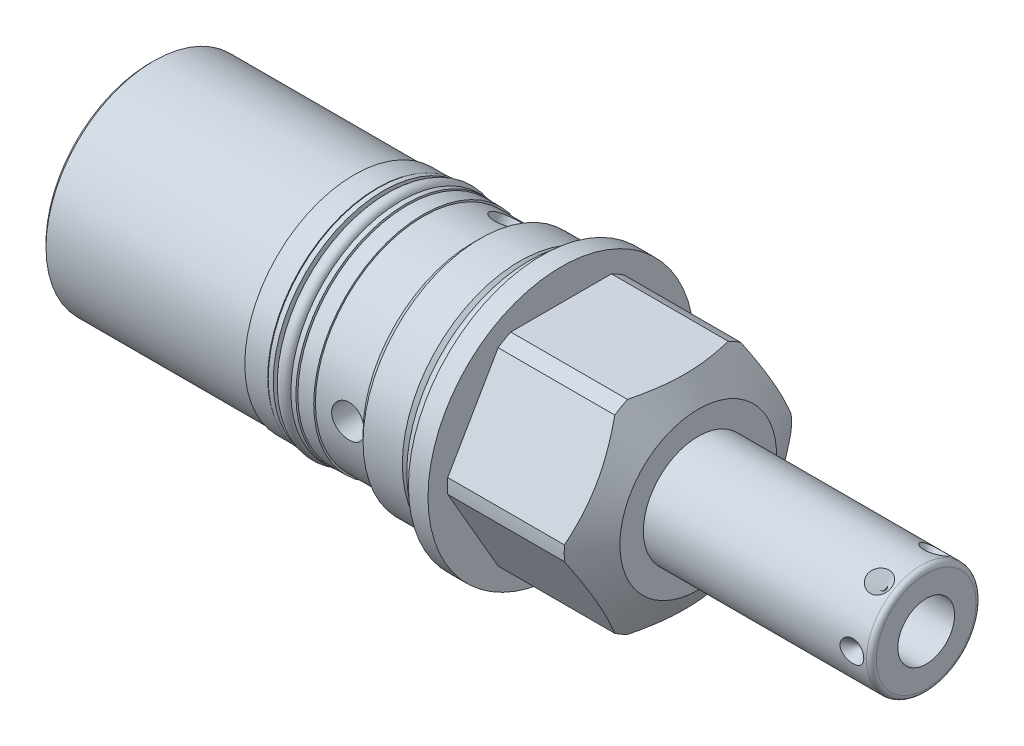
SolidWorks part; units mm, degrees
material "Alloy Steel"
ref_plane "Front Plane" through (0, 0, 0) normal (0, 0, 1) x (1, 0, 0)
ref_plane "Top Plane" through (0, 0, 0) normal (0, 1, 0) x (1, 0, 0)
ref_plane "Right Plane" through (0, 0, 0) normal (1, 0, 0) x (0, 0, -1)
sketch "Sketch1" plane through (0, 0, 0) normal (0, 0, 1) x (1, 0, 0)
  line L0 (0, 0) -> (113.8544, 0) construction
  line L1 (0, 26.9875) -> (3.9624, 26.9875)
  line L2 (3.9624, 26.9875) -> (3.9624, 23.0251)
  line L3 (3.9624, 23.0251) -> (27.6219, 23.0251)
  line L4 (27.6219, 23.0251) -> (31.75, 15.875)
  line L5 (31.75, 15.875) -> (31.75, 0)
  line L6 (31.75, 0) -> (-79.375, 0)
  line L7 (-79.375, 0) -> (-79.375, 21.844)
  line L8 (0, 26.9875) -> (0, 22.3012)
  line L9 (0, 22.3012) -> (-2.8956, 22.3012)
  line L10 (-2.8956, 22.3012) -> (-4.4069, 23.8125)
  line L11 (-4.4069, 23.8125) -> (-12.3698, 23.8125)
  line L12 (-12.3698, 23.8125) -> (-13.9954, 22.1869)
  line L14 (-13.9954, 22.1869) -> (-13.9954, 21.844)
  line L15 (-13.9954, 21.844) -> (-79.375, 21.844)
  dimension "D1" = 53.975
  dimension "D2" = 31.75
  dimension "D3" = 3.9624
  dimension "D4" = 31.75
  dimension "D5" = 46.0502
  dimension "D6" = 30
  dimension "D7" = 79.375
  dimension "D8" = 76.4794
  dimension "D9" = 44.6024
  dimension "D10" = 45
  dimension "D11" = 47.625
  dimension "D12" = 11.0998
  dimension "D13" = 44.3738
  dimension "D14" = 43.688
revolve "Revolve1" add sketch "Sketch1" angle 360 about L0
sketch "Sketch2" plane through (31.75, 0, 0) normal (1, 0, 0) x (0, 0, -1)
  line L1 (11.9151, 20.6375) -> (-11.9151, 20.6375)
  line L2 (-11.9151, 20.6375) -> (-23.8301, 0)
  line L3 (-23.8301, 0) -> (-11.9151, -20.6375)
  line L4 (-11.9151, -20.6375) -> (11.9151, -20.6375)
  line L5 (11.9151, -20.6375) -> (23.8301, 0)
  line L6 (23.8301, 0) -> (11.9151, 20.6375)
  circle A0 centre (0, 0) radius 20.6375 construction
  dimension "D1" = 41.275
extrude "Cut-Extrude1" cut sketch "Sketch2" against normal up to surface (27.7876 mm away) flip side to cut up to face at (3.9624, 0, 26.9875)
sketch "Sketch3" plane through (0, 0, 0) normal (0, 0, 1) x (1, 0, 0)
  line L0 (0, 0) -> (52.5154, 0) construction
  line L1 (31.75, 11.1125) -> (76.962, 11.1125)
  line L2 (31.75, -15.875) -> (31.75, 15.875) construction
  line L3 (77.978, 10.0965) -> (77.978, 0)
  line L4 (77.978, 0) -> (31.75, 0)
  line L5 (31.75, 0) -> (31.75, 11.1125)
  line L6 (0, 26.9875) -> (0, -26.9875) construction
  arc A0 (77.978, 10.0965) -> (76.962, 11.1125) centre (76.962, 10.0965) ccw
  dimension "D1" = 1.016
  dimension "D2" = 77.978
  dimension "D3" = 22.225
revolve "Revolve2" add sketch "Sketch3" angle 360 about L0
sketch "Sketch4" plane through (0, 0, 0) normal (0, 1, 0) x (1, 0, 0)
  line L0 (74.0156, 10.0738) -> (74.0156, 0) construction
  line L1 (77.978, -10.0965) -> (77.978, 10.0965) construction
  line L2 (76.4286, 11.1125) -> (74.0156, 11.1125)
  line L3 (76.962, 11.1125) -> (31.75, 11.1125) construction
  line L4 (74.0156, 11.1125) -> (74.0156, 8.6995)
  line L5 (74.0156, 8.6995) -> (76.4286, 11.1125)
  dimension "D1" = 3.9624
  dimension "D2" = 45
  dimension "D3" = 4.826
revolve "Cut-Revolve1" cut sketch "Sketch4" angle 360 about L0
pattern_circular "CirPattern1" count 6 over 360 about axis through (0, 0, 0) along (-1, 0, 0) of "Cut-Revolve1"
sketch "Sketch5" plane through (0, 0, 0) normal (0, 0, 1) x (1, 0, 0)
  line L0 (0, 0) -> (44.9273, 0) construction
  line L1 (77.978, 5.7531) -> (60.96, 5.7531)
  line L2 (77.978, -10.0965) -> (77.978, 10.0965) construction
  line L3 (60.96, 5.7531) -> (57.5032, 0)
  line L4 (57.5032, 0) -> (77.978, 0)
  line L5 (77.978, 0) -> (77.978, 5.7531)
  dimension "D1" = 17.018
  dimension "D2" = 59
  dimension "D3" = 11.5062
revolve "Cut-Revolve2" cut sketch "Sketch5" angle 360 about L0
sketch "Sketch6" plane through (0, 0, 0) normal (0, 0, 1) x (1, 0, 0)
  line L0 (-24.003, 21.844) -> (-24.003, 22.1869)
  line L1 (-13.9954, 21.844) -> (-79.375, 21.844) construction
  line L2 (-24.003, 22.1869) -> (-37.973, 22.1869)
  line L3 (-37.973, 22.1869) -> (-37.973, 21.844)
  line L4 (-37.973, 21.844) -> (-24.003, 21.844)
  line L5 (0, 0) -> (-62.9111, 0) construction
  line L6 (-79.375, 21.844) -> (-79.375, -21.844) construction
  dimension "D1" = 13.97
  dimension "D2" = 44.3738
  dimension "D3" = 41.402
revolve "Revolve3" add sketch "Sketch6" angle 360 about L5
sketch "Sketch7" plane through (-79.375, 0, 0) normal (-1, 0, 0) x (0, 0, 1)
  circle A0 centre (0, 0) radius 3.1369
  dimension "D1" = 6.2738
extrude "Cut-Extrude2" cut sketch "Sketch7" against normal blind 0.762
sketch "Sketch8" plane through (0, 0, 0) normal (0, 0, 1) x (1, 0, 0)
  line L0 (0, 0) -> (-56.7277, 0) construction
  line L1 (-24.003, 22.1869) -> (-37.973, 22.1869) construction
  line L2 (-33.3248, 22.1869) -> (-27.2161, 22.1869)
  line L3 (-33.3248, 22.1869) -> (-33.3248, 20.1549)
  line L4 (-33.3248, 20.1549) -> (-27.2161, 20.1549)
  line L5 (-27.2161, 22.1869) -> (-27.2161, 20.1549)
  line L6 (-79.375, 21.844) -> (-79.375, -21.844) construction
  dimension "D1" = 6.1087
  dimension "D2" = 46.0502
  dimension "D3" = 40.3098
revolve "Cut-Revolve3" cut sketch "Sketch8" angle 360 about L0
sketch "Sketch9" plane through (0, 0, 0) normal (0, 0, 1) x (1, 0, 0)
  line L0 (0, 0) -> (-59.2046, 0) construction
  line L1 (-30.2705, 14.9069) -> (-30.2705, -14.8344) construction
  line L2 (-33.3248, -22.1869) -> (-33.3248, 22.1869) construction
  line L3 (-27.2161, 20.1549) -> (-27.2161, -20.1549) construction
  line L4 (-27.2161, 20.1549) -> (-33.3248, 20.1549) construction
  line L5 (-28.4861, 22.3393) -> (-27.4701, 22.3393)
  line L6 (-28.4861, 22.3393) -> (-28.4861, 20.1549)
  line L7 (-28.4861, 20.1549) -> (-27.4701, 20.1549)
  line L8 (-27.4701, 22.3393) -> (-27.4701, 20.1549)
  line L9 (-27.2161, 22.1869) -> (-27.2161, -22.1869) construction
  line L10 (-33.0708, 22.3393) -> (-33.0708, 20.1549)
  line L11 (-32.0548, 20.1549) -> (-33.0708, 20.1549)
  line L12 (-32.0548, 22.3393) -> (-32.0548, 20.1549)
  line L13 (-32.0548, 22.3393) -> (-33.0708, 22.3393)
  dimension "D1" = 1.016
  dimension "D2" = 0.254
  dimension "D3" = 2.1844
revolve "Revolve4" add sketch "Sketch9" angle 360 about L0
sketch "Sketch10" plane through (0, 0, 0) normal (0, 1, 0) x (1, 0, 0)
  line L0 (-17.399, 23.0369) -> (-17.399, -3.4735) construction
  line L1 (-79.375, 21.844) -> (-79.375, -21.844) construction
  line L2 (-17.399, -23.8125) -> (-20.7137, -23.8125)
  line L4 (-20.7137, -23.8125) -> (-20.7137, -11.1125)
  line L5 (-20.7137, -11.1125) -> (-17.399, -11.1125)
  line L6 (-17.399, -11.1125) -> (-17.399, -23.8125)
  line L8 (-12.3698, -23.8125) -> (-4.4069, -23.8125) construction
  dimension "D1" = 61.976
  dimension "D2" = 6.6294
  dimension "D3" = 11.1125
revolve "Cut-Revolve4" cut sketch "Sketch10" angle 360 about L0
pattern_circular "CirPattern2" count 3 over 360 about axis through (0, 0, 0) along (1, 0, 0) of "Cut-Revolve4"
chamfer "Chamfer1" distance 0.762 angle 45 1 edges at (-79.375, 0, 21.844)
sketch "Sketch11" plane through (0, 0, 0) normal (0, 0, 1) x (1, 0, 0)
  line L0 (0, 0) -> (23.6366, 0) construction
  line L1 (0, 26.9875) -> (0, -26.9875) construction
  line L2 (0, 22.3012) -> (-2.8956, 22.3012) construction
  circle A0 centre (-1.4732, 23.7744) radius 1.4732
  dimension "D1" = 2.9464
  dimension "D2" = 47.5488
revolve "Revolve5" add sketch "Sketch11" angle 360 about L0
sketch "Sketch12" plane through (0, 0, 0) normal (0, 0, 1) x (1, 0, 0)
  line L0 (0, 0) -> (-56.0967, 0) construction
  line L1 (-28.4861, 20.1549) -> (-32.0548, 20.1549) construction
  line L2 (-30.2704, 21.463) -> (-30.2704, 6.0377) construction
  line L3 (-33.3248, -22.1869) -> (-33.3248, 22.1869) construction
  line L4 (-27.2161, 20.1549) -> (-27.2161, -20.1549) construction
  circle A0 centre (-30.2704, 21.463) radius 1.3081
  dimension "D1" = 2.6162
revolve "Revolve7" add sketch "Sketch12" angle 360 about L0
sketch "Sketch13" plane through (0, 0, 0) normal (0, 0, 1) x (1, 0, 0)
  line L0 (-63.2754, 0) -> (0, 0) construction
  line L1 (-79.375, 6.1849) -> (-76.8096, 5.6396)
  line L2 (-79.375, 21.082) -> (-79.375, -21.082) construction
  line L3 (-76.8096, 5.6396) -> (-76.1484, 4.9784)
  line L4 (-76.1484, 4.9784) -> (-65.1002, 4.9784)
  line L5 (-65.1002, 4.9784) -> (-65.1002, 0)
  line L6 (-65.1002, 0) -> (-79.375, 0)
  line L7 (-79.375, 0) -> (-79.375, 6.1849)
  dimension "D1" = 12
  dimension "D2" = 12.3698
  dimension "D3" = 45
  dimension "D4" = 2.5654
  dimension "D5" = 9.9568
  dimension "D6" = 14.2748
revolve "Cut-Revolve5" cut sketch "Sketch13" angle 360 about L0
sketch "Sketch14" plane through (-79.375, 0, 0) normal (-1, 0, 0) x (0, 0, 1)
  circle A0 centre (0, 0) radius 17.7927
extrude "Extrude1" add sketch "Sketch14" along normal blind 0.508
sketch "Sketch15" plane through (-79.883, 0, 0) normal (-1, 0, 0) x (0, 0, 1)
  circle A0 centre (0, 0) radius 6.1849
extrude "Cut-Extrude3" cut sketch "Sketch15" against normal blind 0.508
